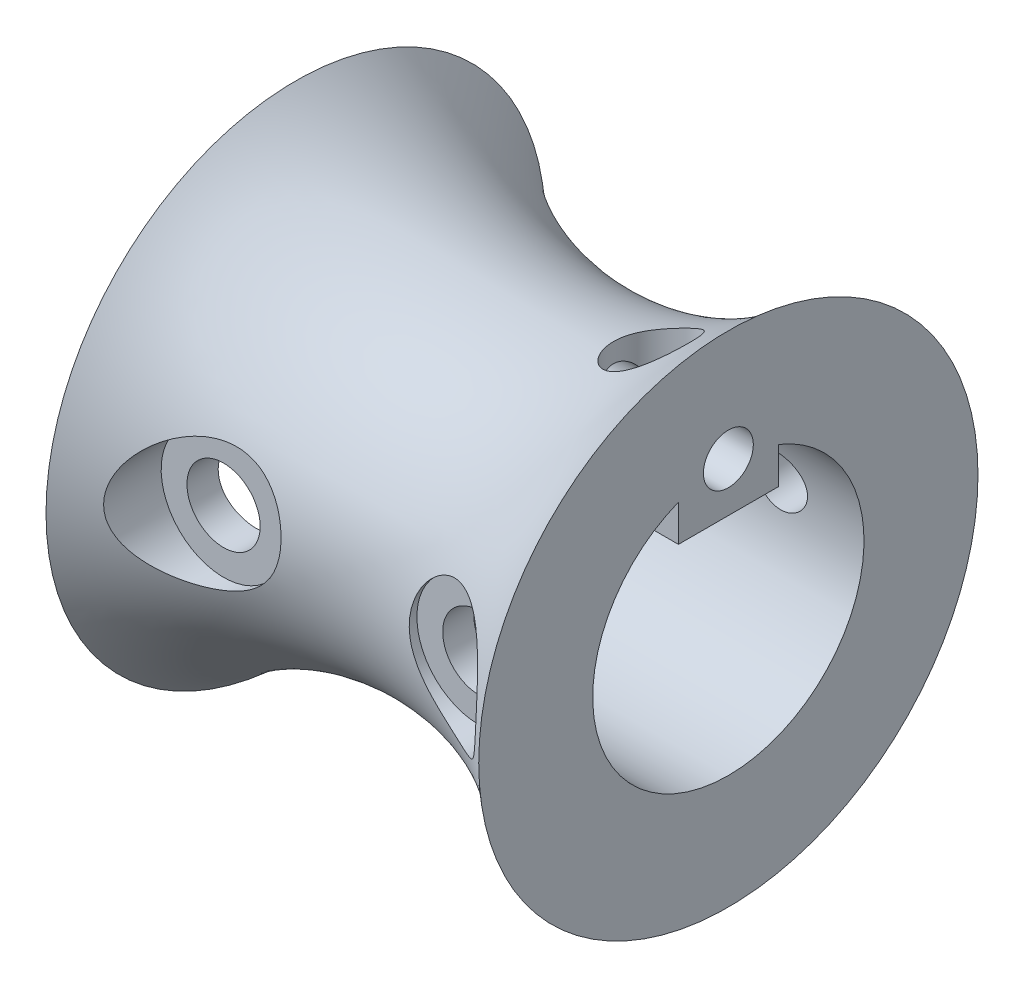
SolidWorks part; units mm, degrees
ref_plane "Front Plane" through (0, 0, 0) normal (0, 0, 1) x (1, 0, 0)
ref_plane "Top Plane" through (0, 0, 0) normal (0, 1, 0) x (1, 0, 0)
ref_plane "Right Plane" through (0, 0, 0) normal (1, 0, 0) x (0, 0, -1)
sketch "Sketch1" plane through (0, 0, 0) normal (0, 0, 1) x (1, 0, 0)
  line L0 (-6.7553, -0.3731) -> (6.2447, -0.3731)
  line L1 (-6.7553, -0.3731) -> (-6.7553, 7.1269)
  line L2 (6.2447, -0.3731) -> (6.2447, 7.1269)
  line L3 (6.2447, 7.1269) -> (-6.7553, 7.1269) construction
  line L4 (-6.7553, 7.1269) -> (-6.9633, 7.1402) construction
  arc A0 (-6.7553, 7.1269) -> (6.2447, 7.1269) centre (-0.2553, 14.3269) ccw
  point P5 (-0.2553, 4.6269)
  dimension "D1" = 13
  dimension "D3" = 5
  dimension "D2" = 7.5
revolve "Revolve1" add sketch "Sketch1" angle 360 about L0
ref_plane "Plane1" through (0, 7.1269, 0) normal (0, 1, 0) x (1, 0, 0)
sketch "Sketch2" plane through (-6.7553, 0, 0) normal (-1, 0, 0) x (0, 0, 1)
  line L0 (0, 3.6019) -> (0, 2.3158) construction
  line L1 (1.5, 3.3158) -> (-1.5, 3.3158) construction
  line L2 (1.5, 3.3158) -> (1.5, 2.3158)
  line L3 (1.5, 2.3158) -> (-1.5, 2.3158)
  line L4 (-1.5, 3.3158) -> (-1.5, 2.3158)
  line L5 (1.5, 3.3158) -> (1.5, 3.4158)
  line L6 (1.5, 3.4158) -> (-1.5, 3.4158) construction
  line L7 (-1.5, 3.4158) -> (-1.5, 3.3158)
  circle A0 centre (0, -0.3731) radius 3.975 construction
  arc A1 (-1.5, 3.4158) -> (1.5, 3.4158) centre (0, -0.3731) ccw
  circle A2 centre (0, -0.3731) radius 7.5 construction
  circle A4 centre (0, -0.3731) radius 7.5 construction
  dimension "D3" = 4.075
  dimension "D1" = 3
  dimension "D2" = 0.1
  dimension "D4" = 1
extrude "Cut-Extrude1" cut sketch "Sketch2" against normal through all
sketch "Sketch3" plane through (6.2447, 0, 0) normal (1, 0, 0) x (0, 0, -1)
  circle A0 centre (0, 3.7908) radius 0.75
  dimension "D1" = 1.5
extrude "cable hole" cut sketch "Sketch3" against normal through all
sketch "Sketch4" plane through (0, 7.1269, 0) normal (0, 1, 0) x (1, 0, 0)
  line L0 (6.2447, -0.75) -> (6.2447, 0.75) construction
  line L1 (6.2447, -0.75) -> (6.2447, 0.75) construction
  line L2 (3.9235, 0) -> (6.2447, 0) construction
  circle A0 centre (3.9235, 0) radius 1.1303
  dimension "D1" = 2.2606
extrude "5-40 set screw hole" cut sketch "Sketch4" against normal blind 3
ref_plane "Plane2" through (0, 0, 7.5) normal (0, 0, 1) x (1, 0, 0)
sketch "Sketch6" plane through (0, 0, 7.5) normal (0, 0, 1) x (1, 0, 0)
  circle A0 centre (3.7627, 0) radius 0.8
  circle A1 centre (-3.9208, 0) radius 0.8
  dimension "D1" = 1.6
extrude "M2 X 0.4 screw hole" cut sketch "Sketch6" against normal through all
sketch "Sketch7" plane through (0, 0, 7.5) normal (0, 0, 1) x (1, 0, 0)
  circle A0 centre (3.7627, 0) radius 1.1
  circle A1 centre (-3.9208, 0) radius 1.1
  dimension "D1" = 2.2
extrude "hole for cap screw" cut sketch "Sketch7" against normal blind 5
sketch "Sketch8" plane through (0, 0, 7.5) normal (0, 0, 1) x (1, 0, 0)
  circle A0 centre (3.7627, 0) radius 1.875
  circle A1 centre (-3.9208, 0) radius 1.875
  dimension "D1" = 3.75
extrude "Cut-Extrude6" cut sketch "Sketch8" against normal blind 2.5
sketch "Sketch9" plane through (0, 7.1269, 0) normal (0, 1, 0) x (1, 0, 0)
  line L1 (-9.7291, 2.0046) -> (18.4099, 2.0046)
  line L2 (-9.7291, 2.0046) -> (-9.7291, 9.1328)
  line L3 (-9.7291, 9.1328) -> (18.4099, 9.1328)
  line L4 (18.4099, 2.0046) -> (18.4099, 9.1328)
extrude "Cut-Extrude7" [suppressed] cut sketch "Sketch9" against normal through all
